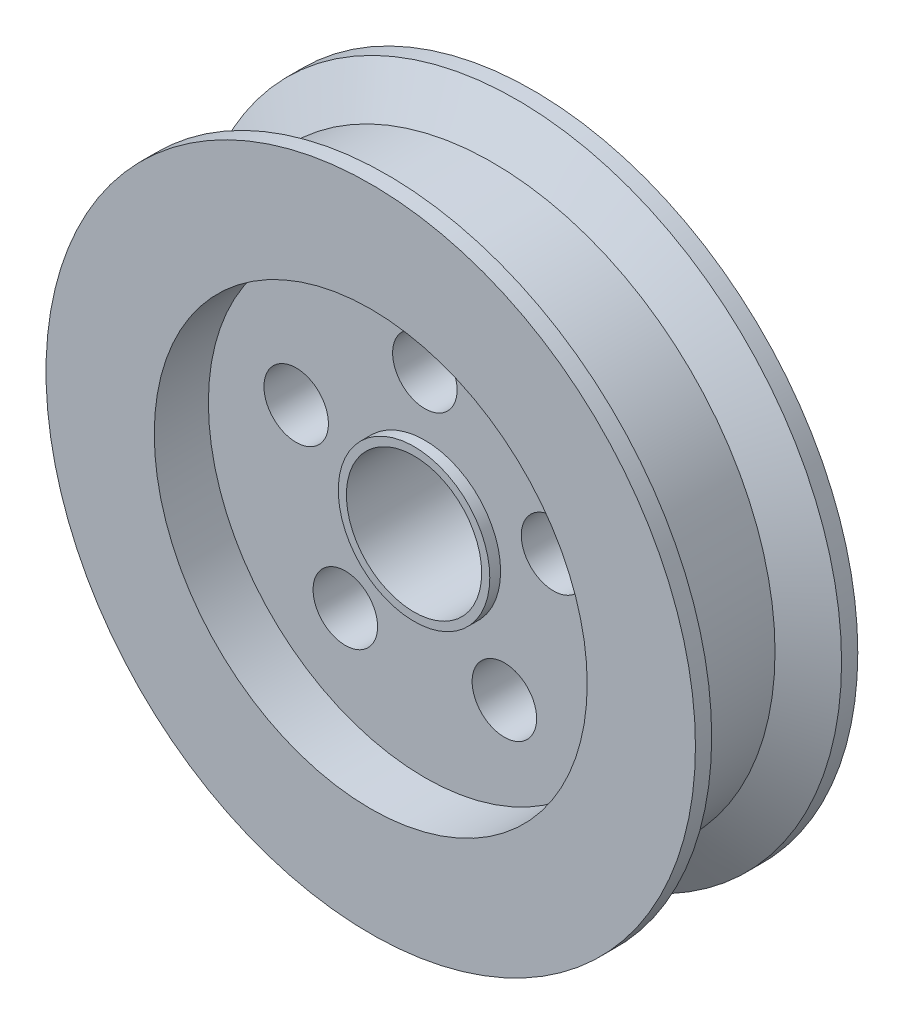
SolidWorks part; units mm, degrees
ref_plane "Front Plane" through (0, 0, 0) normal (0, 0, 1) x (1, 0, 0)
ref_plane "Top Plane" through (0, 0, 0) normal (0, 1, 0) x (1, 0, 0)
ref_plane "Right Plane" through (0, 0, 0) normal (1, 0, 0) x (0, 0, -1)
sketch "Sketch1" plane through (0, 0, 0) normal (0, 0, 1) x (1, 0, 0)
  circle A0 centre (0, 0) radius 60
  circle A1 centre (0, 0) radius 12.5
  dimension "D1" = 120
  dimension "D2" = 25
extrude "Boss-Extrude2" add sketch "Sketch1" along normal blind 30
sketch "Sketch3" plane through (0, 0, 30) normal (0, 0, 1) x (1, 0, 0)
  circle A0 centre (0, 0) radius 40
  dimension "D1" = 80
extrude "Cut-Extrude3" cut sketch "Sketch3" against normal blind 10
mirror "Mirror6" about plane through (0, 0, 0) normal (0, 0, 1) of "Cut-Extrude3"
sketch "Sketch4" plane through (0, 0, 20) normal (0, 0, 1) x (1, 0, 0)
  circle A0 centre (0, 25) radius 5.9591
  circle A1 centre (23.7764, 7.7254) radius 5.9591
  circle A2 centre (14.6946, -20.2254) radius 5.9591
  circle A3 centre (-14.6946, -20.2254) radius 5.9591
  circle A4 centre (-23.7764, 7.7254) radius 5.9591
  point P13 (0, 0)
  dimension "D1" = 25
  dimension "D2" = 5
extrude "Cut-Extrude4" cut sketch "Sketch4" against normal through all
sketch "Sketch6" plane through (0, 0, 0) normal (0, 1, 0) x (1, 0, 0)
  line L0 (0, 0) -> (0, 21.2727) construction
  line L1 (60, -3) -> (52.2058, -7.5)
  line L2 (60, -30) -> (60, 0) construction
  line L3 (52.2058, -7.5) -> (52.2058, -22.5)
  line L4 (52.2058, -22.5) -> (60, -27)
  line L5 (60, -3) -> (60, -27)
  dimension "D1" = 3
  dimension "D2" = 3
  dimension "D3" = 60
  dimension "D4" = 60
  dimension "D5" = 15
revolve "Cut-Revolve1" cut sketch "Sketch6" angle 360 about L0
sketch "Sketch7" plane through (0, 0, 20) normal (0, 0, 1) x (1, 0, 0)
  circle A0 centre (0, 0) radius 14.2032
  circle A2 centre (0, 0) radius 14
  circle A3 centre (0, 0) radius 12.5
  circle M6 centre (0, 0) radius 12.5
  dimension "D1" = 28.4063
extrude "Boss-Extrude6" add sketch "Sketch7" along normal blind 2 and the other way blind 7 contours A2 M6
